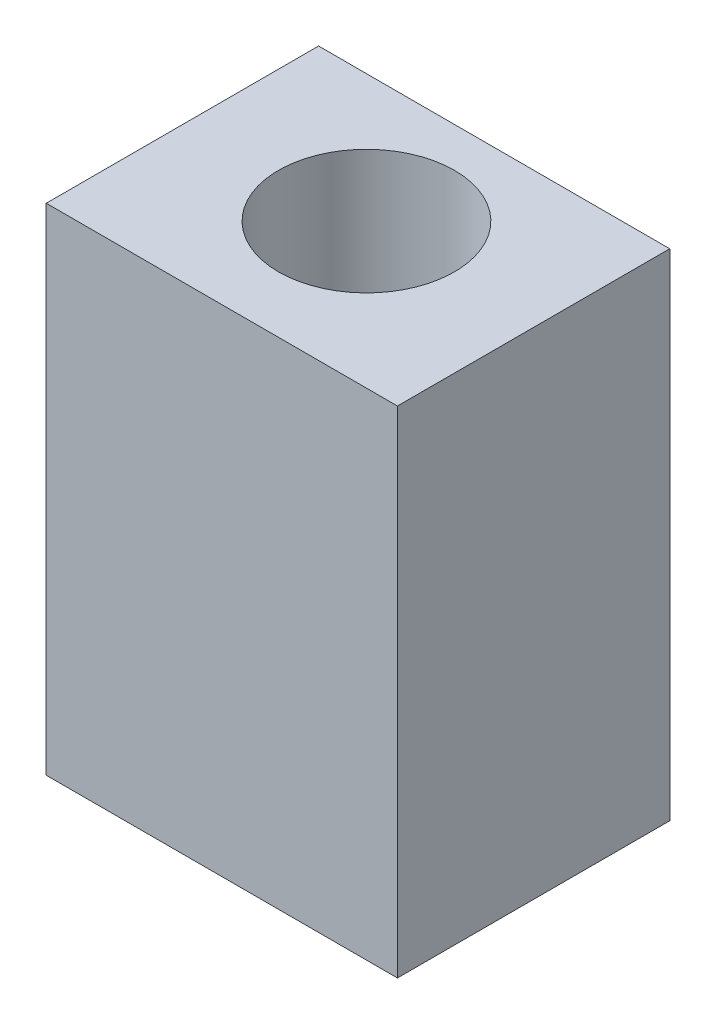
SolidWorks part; units mm, degrees
material "6061-T6 (SS)"
ref_plane "Front Plane" through (0, 0, 0) normal (0, 0, 1) x (1, 0, 0)
ref_plane "Top Plane" through (0, 0, 0) normal (0, 1, 0) x (1, 0, 0)
ref_plane "Right Plane" through (0, 0, 0) normal (1, 0, 0) x (0, 0, -1)
sketch "Sketch1" plane through (0, 0, 0) normal (0, 1, 0) x (1, 0, 0)
  line L1 (-20.955, -16.25) -> (20.955, -16.25)
  line L2 (-20.955, -16.25) -> (-20.955, 16.25)
  line L3 (-20.955, 16.25) -> (20.955, 16.25)
  line L4 (20.955, -16.25) -> (20.955, 16.25)
  line L5 (-20.955, -16.25) -> (20.955, 16.25) construction
  line L6 (-20.955, 16.25) -> (20.955, -16.25) construction
  point P0 (0, 0)
  dimension "D1" = 41.91
  dimension "D2" = 32.5
extrude "Boss-Extrude1" add sketch "Sketch1" along normal blind 59.1185
sketch "Sketch2" plane through (0, 59.1185, 0) normal (0, 1, 0) x (1, 0, 0)
  line L0 (0, -55) -> (0, 55) construction
  line L1 (20.955, 16.25) -> (-20.955, 16.25) construction
  circle A0 centre (0, 1.01) radius 10.5
  dimension "D1" = 21
  dimension "D2" = 15.24
extrude "Cut-Extrude1" cut sketch "Sketch2" against normal through all
hole_wizard "#10-32 Tapped Hole1" positions "Sketch3" profile "Sketch4" tap size "#10-32" standard "ANSI Inch"
sketch "Sketch3" plane through (0, 0, -16.25) normal (0, 0, -1) x (-1, 0, 0)
  line L0 (-14.986, 44.7993) -> (-14.986, 14.3193) construction
  line L2 (-20.955, 59.1185) -> (-20.955, 0) construction
  line L3 (20.955, 59.1185) -> (20.955, 0) construction
  point P0 (-14.986, 14.3193)
  point P2 (14.986, 14.3193)
  point P4 (14.986, 44.7993)
  point P6 (-14.986, 44.7993)
  point P17 (-14.986, 29.5593)
  point P20 (-20.955, 29.5593)
  point P21 (0, 0)
  point P22 (0, 0)
  dimension "D1" = 30.48
  dimension "D2" = 5.969
  dimension "D3" = 5.969
sketch "Sketch4" plane through (14.986, 14.3193, -16.25) normal (1, 0, 0) x (0, 1, 0)
  line L0 (0, 0) -> (0, 11.1193)
  line L1 (0, 11.1193) -> (2.0193, 9.906)
  line L2 (2.0193, 9.906) -> (2.0193, 0)
  line L5 (2.0193, 0) -> (0, 0)
  line L10 (0, 11.1193) -> (-2.0193, 9.906) construction
  line L11 (0, -6.35) -> (0, 107.95) construction
  dimension "Tap Drill Dia." = 4.0386
  dimension "Tap Drill Depth" = 9.906
  dimension "Drill Angle" = 118
cosmetic thread "Hole Thread1" parameters "D1"=7.62, "D2"=4.826
cosmetic thread "Hole Thread2" parameters "D1"=7.62, "D2"=4.826
cosmetic thread "Hole Thread3" parameters "D1"=7.62, "D2"=4.826
cosmetic thread "Hole Thread4" parameters "D1"=7.62, "D2"=4.826
